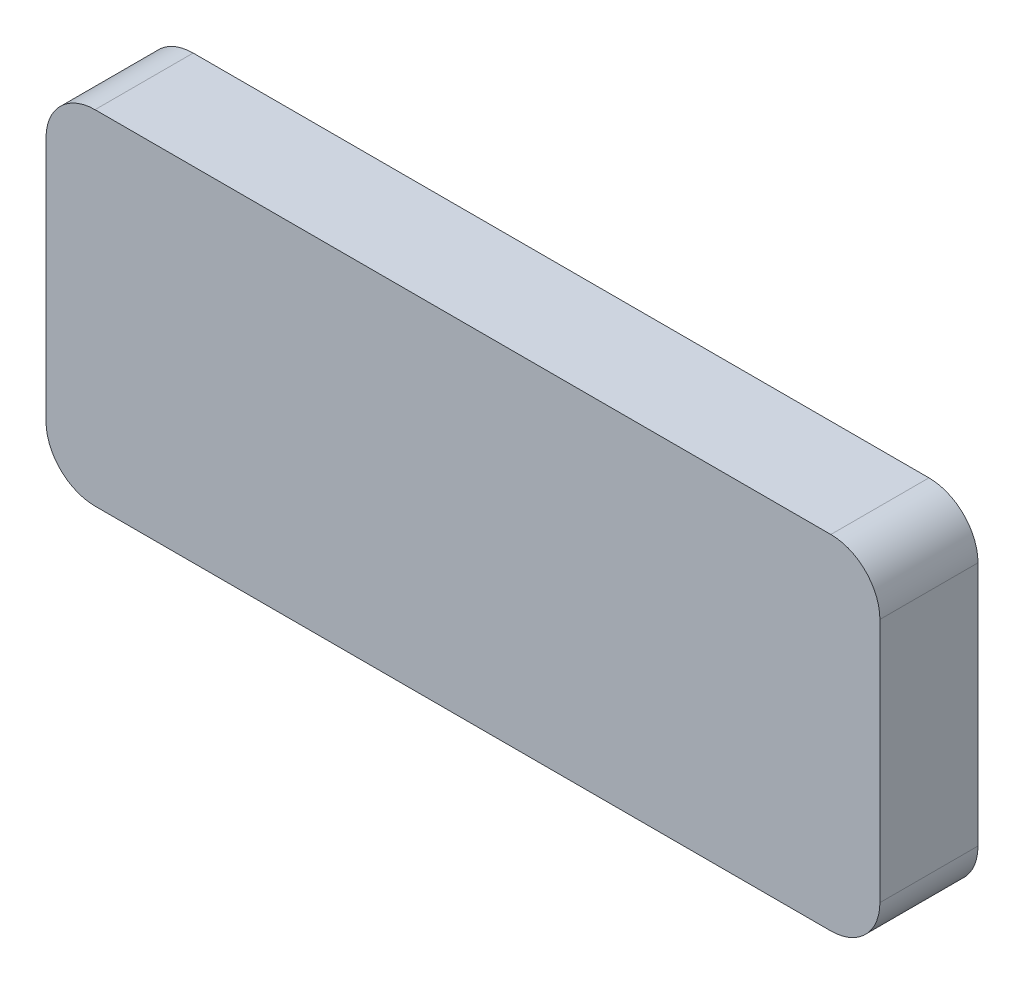
SolidWorks part; units mm, degrees
ref_plane "Front Plane" through (0, 0, 0) normal (0, 0, 1) x (1, 0, 0)
ref_plane "Top Plane" through (0, 0, 0) normal (0, 1, 0) x (1, 0, 0)
ref_plane "Right Plane" through (0, 0, 0) normal (1, 0, 0) x (0, 0, -1)
sketch "Sketch1" plane through (0, 0, 0) normal (0, 0, 1) x (1, 0, 0)
  line L1 (8.5, -3.5) -> (-8.5, -3.5)
  line L2 (8.5, -3.5) -> (8.5, 3.5)
  line L3 (8.5, 3.5) -> (-8.5, 3.5)
  line L4 (-8.5, -3.5) -> (-8.5, 3.5)
  line L5 (8.5, -3.5) -> (-8.5, 3.5) construction
  line L6 (8.5, 3.5) -> (-8.5, -3.5) construction
  point P0 (0, 0)
  dimension "D1" = 17
  dimension "D2" = 7
extrude "Extrude1" add sketch "Sketch1" along normal blind 2
fillet "Fillet1" radius 1 4 edges at (-8.5, -3.5, 1) (8.5, -3.5, 1) (8.5, 3.5, 1) (-8.5, 3.5, 1)
